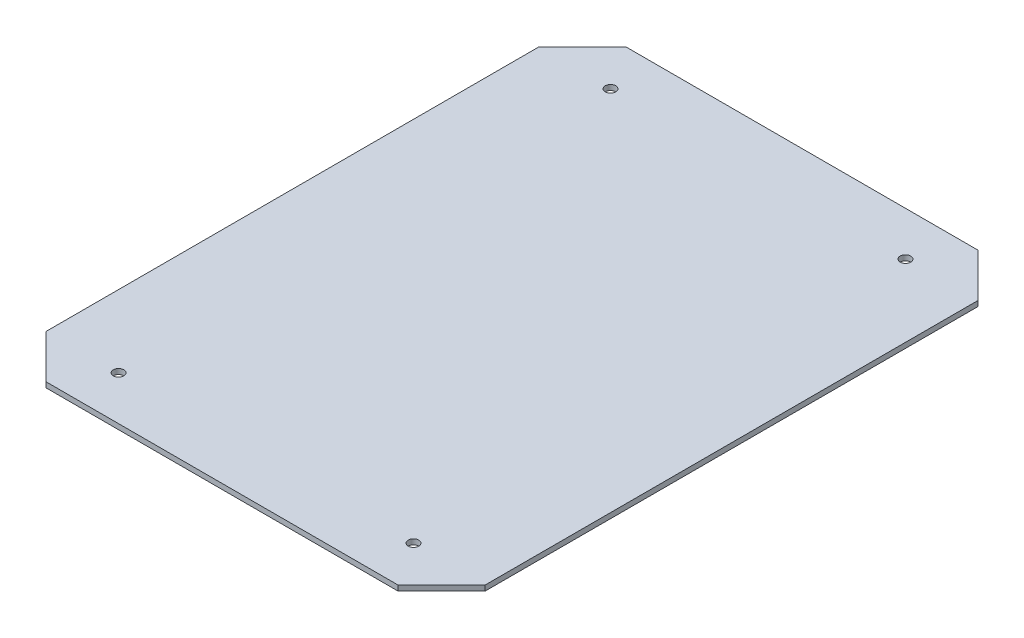
SolidWorks part; units mm, degrees
ref_plane "Plan de face" through (0, 0, 0) normal (0, 0, 1) x (1, 0, 0)
ref_plane "Plan de dessus" through (0, 0, 0) normal (0, 1, 0) x (1, 0, 0)
ref_plane "Plan de droite" through (0, 0, 0) normal (1, 0, 0) x (0, 0, -1)
sketch "Esquisse1" plane through (0, 0, 0) normal (0, 1, 0) x (1, 0, 0)
  line L0 (100, -164.7487) -> (-100, -164.7487)
  line L1 (-100, -164.7487) -> (-124.7487, -140)
  line L2 (-124.7487, -140) -> (-124.7487, 140)
  line L3 (-124.7487, 140) -> (-100, 164.7487)
  line L4 (-100, 164.7487) -> (100, 164.7487)
  line L5 (100, 164.7487) -> (124.7487, 140)
  line L6 (124.7487, 140) -> (124.7487, -140)
  line L7 (124.7487, -140) -> (100, -164.7487)
  line L8 (-100, 164.7487) -> (100, -164.7487) construction
  point P8 (0, 0)
  dimension "D1" = 280
  dimension "D2" = 35
  dimension "D3" = 135
  dimension "D4" = 200
extrude "Boss.-Extru.1" add sketch "Esquisse1" along normal blind 3
sketch "Esquisse2" plane through (0, 3, 0) normal (0, 1, 0) x (1, 0, 0)
  line L0 (100, 164.7487) -> (-100, 164.7487) construction
  line L1 (0, 164.7487) -> (0, -164.7487) construction
  line L2 (-100, -164.7487) -> (100, -164.7487) construction
  line L3 (-124.7487, 0) -> (124.7487, 0) construction
  line L4 (-124.7487, 140) -> (-124.7487, -140) construction
  line L5 (124.7487, -140) -> (124.7487, 140) construction
  line L6 (-93.7868, 149.7487) -> (-73.7868, 149.7487) construction
  line L7 (-73.7868, 149.7487) -> (-73.7868, 129.7487) construction
  line L8 (-73.7868, 129.7487) -> (-93.7868, 129.7487) construction
  line L9 (-93.7868, 129.7487) -> (-93.7868, 149.7487) construction
  line L10 (-93.7868, 149.7487) -> (-73.7868, 129.7487) construction
  line L12 (-100, 164.7487) -> (-124.7487, 140) construction
  circle A0 centre (-83.7868, 139.7487) radius 3
  circle A1 centre (83.7868, 139.7487) radius 3
  circle A2 centre (83.7868, -139.7487) radius 3
  circle A3 centre (-83.7868, -139.7487) radius 3
  point P14 (-83.7868, 139.7487)
  dimension "D1" = 6
  dimension "D2" = 15
  dimension "D3" = 15
  dimension "D4" = 20
extrude "Enlèv. mat.-Extru.1" cut sketch "Esquisse2" against normal through all
sketch "Esquisse3" plane through (0, 3, 0) normal (0, 1, 0) x (1, 0, 0)
  line L0 (-79.7487, -104.7487) -> (-79.7487, -89.7487) construction
  line L1 (-79.7487, -104.7487) -> (-79.7487, -119.7487) construction
  line L4 (-100, -164.7487) -> (100, -164.7487) construction
  line L5 (-124.7487, 140) -> (-124.7487, -140) construction
  circle A0 centre (-79.7487, -119.7487) radius 2
  circle A1 centre (-79.7487, -89.7487) radius 2
  circle A2 centre (-79.7487, -104.7487) radius 11
  point P12 (-62.4137, -164.7487)
  dimension "D1" = 22
  dimension "D2" = 4
  dimension "D3" = 15
  dimension "D4" = 15
  dimension "D5" = 45
  dimension "D6" = 60
